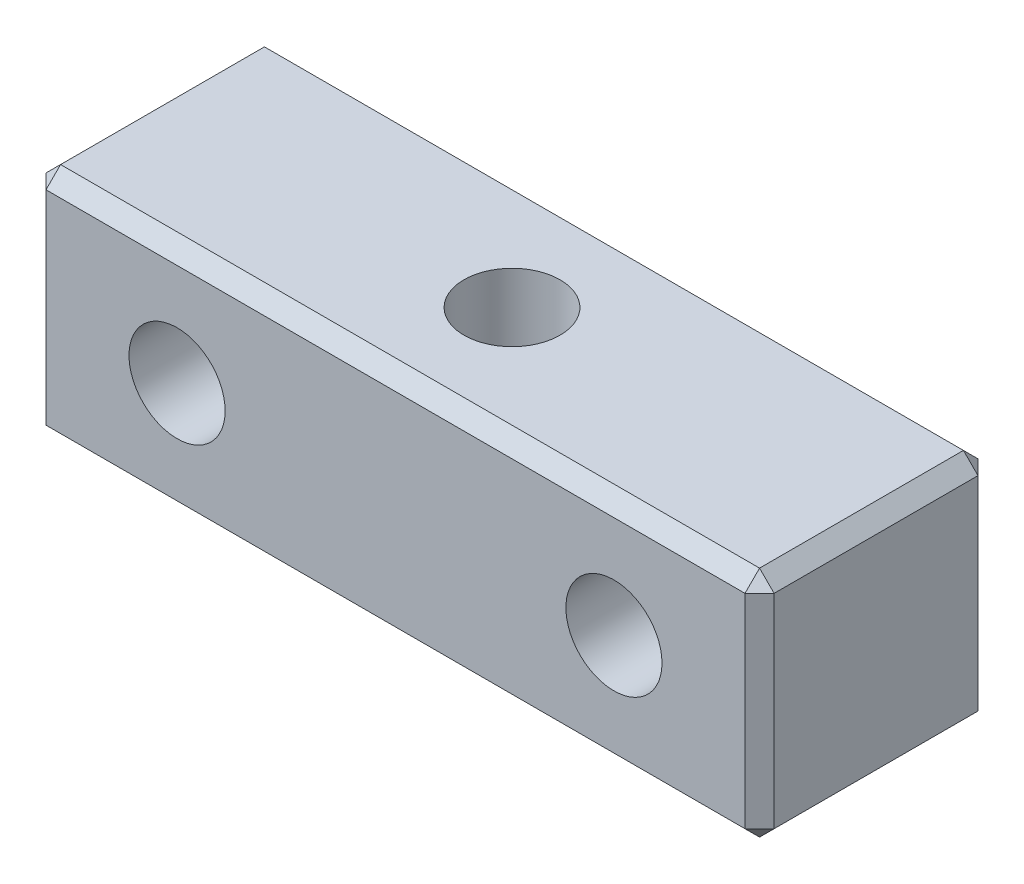
SolidWorks part; units mm, degrees
material "6063-T5"
ref_plane "前视基准面" through (0, 0, 0) normal (0, 0, 1) x (1, 0, 0)
ref_plane "上视基准面" through (0, 0, 0) normal (0, 1, 0) x (1, 0, 0)
ref_plane "右视基准面" through (0, 0, 0) normal (1, 0, 0) x (0, 0, -1)
other "Configuration Table"
sketch "草图1" plane through (0, 0, 0) normal (0, 0, 1) x (1, 0, 0)
  line L1 (-12.5, -4) -> (12.5, -4)
  line L2 (-12.5, -4) -> (-12.5, 4)
  line L3 (-12.5, 4) -> (12.5, 4)
  line L4 (12.5, -4) -> (12.5, 4)
  line L5 (-12.5, -4) -> (12.5, 4) construction
  line L6 (-12.5, 4) -> (12.5, -4) construction
  point P0 (0, 0)
  dimension "D1" = 8
  dimension "D2" = 25
extrude "凸台-拉伸1" add sketch "草图1" along normal blind 8
chamfer "倒角1" distance 0.5 angle 45 12 edges at (-12.5, 0, 0) (12.5, 0, 0) (-12.5, -4, 4) (0, -4, 0) (12.5, -4, 4) (0, -4, 8) (-12.5, 0, 8) (12.5, 0, 8) (12.5, 4, 4) (0, 4, 8) (-12.5, 4, 4) (0, 4, 0)
sketch "草图2" plane through (0, -4, 0) normal (0, -1, 0) x (1, 0, 0)
  circle A0 centre (0, 4) radius 2.025
  dimension "D1" = 4.05
  dimension "D2" = 4
hole_wizard "M4 螺纹孔1" positions "3D草图2" profile "草图4" tap size "M4" standard "GB" end condition through all
sketch3d "3D草图2"
  point P0 (0, -4, 4)
sketch "草图4" plane through (0, -4, 4) normal (1, 0, 0) x (0, 0, -1)
  line L0 (0, 0) -> (0, 8)
  line L1 (0, 8) -> (1.65, 8)
  line L2 (1.65, 8) -> (1.65, 0)
  line L5 (1.65, 0) -> (0, 0)
  line L11 (0, -6.35) -> (0, 107.95) construction
  dimension "通孔螺纹孔钻头直径" = 3.3
  dimension "通孔螺纹孔钻头深度" = 8
cosmetic thread "孔螺蚊线1" parameters "D2"=4
sketch "草图5" plane through (0, 0, 8) normal (0, 0, 1) x (1, 0, 0)
  line L0 (0, 0) -> (0, 4) construction
  line L1 (-12, 4) -> (12, 4) construction
  circle A0 centre (-7.5, 0) radius 2.025
  circle A1 centre (7.5, 0) radius 2.025
  dimension "D1" = 4.05
  dimension "D2" = 15
hole_wizard "M4 螺纹孔2" positions "3D草图3" profile "草图6" tap size "M4" standard "GB" end condition through all
sketch3d "3D草图3"
  point P0 (-7.5, 0, 8)
  point P3 (7.5, 0, 8)
sketch "草图6" plane through (-7.5, 0, 8) normal (1, 0, 0) x (0, -1, 0)
  line L0 (0, 0) -> (0, 8)
  line L1 (0, 8) -> (1.65, 8)
  line L2 (1.65, 8) -> (1.65, 0)
  line L5 (1.65, 0) -> (0, 0)
  line L11 (0, -6.35) -> (0, 107.95) construction
  dimension "通孔螺纹孔钻头直径" = 3.3
  dimension "通孔螺纹孔钻头深度" = 8
cosmetic thread "孔螺蚊线2" parameters "D2"=4
cosmetic thread "孔螺蚊线3" parameters "D2"=4
